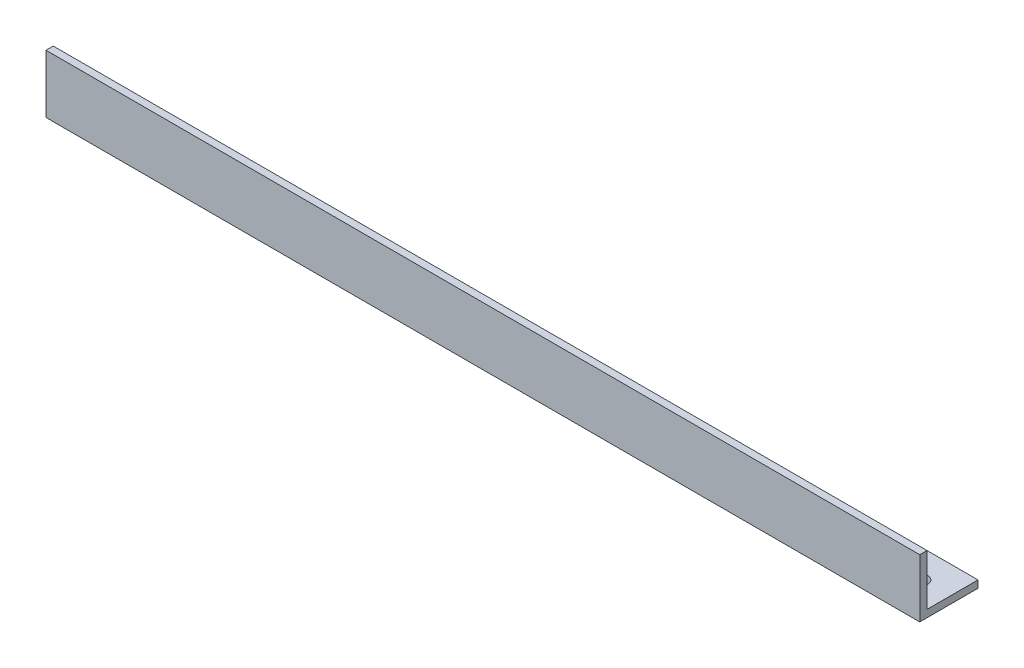
SolidWorks part; units mm, degrees
ref_plane "Front Plane" through (0, 0, 0) normal (0, 0, 1) x (1, 0, 0)
ref_plane "Top Plane" through (0, 0, 0) normal (0, 1, 0) x (1, 0, 0)
ref_plane "Right Plane" through (0, 0, 0) normal (1, 0, 0) x (0, 0, -1)
sketch "Sketch1" plane through (0, 0, 0) normal (1, 0, 0) x (0, 0, -1)
  line L0 (0, 0) -> (25.4, 0)
  line L1 (0, 0) -> (0, 25.4)
  line L2 (0, 25.4) -> (3.175, 25.4)
  line L3 (3.175, 25.4) -> (3.175, 3.175)
  line L4 (3.175, 3.175) -> (25.4, 3.175)
  line L5 (25.4, 3.175) -> (25.4, 0)
  dimension "D1" = 3.175
  dimension "D2" = 3.175
  dimension "D3" = 25.4
  dimension "D4" = 25.4
extrude "Boss-Extrude1" add sketch "Sketch1" along normal blind 381
sketch "Sketch2" plane through (0, 0, 0) normal (0, -1, 0) x (1, 0, 0)
  line L0 (381, 0) -> (381, -25.4) construction
  line L1 (381, -25.4) -> (0, -25.4) construction
  line L2 (0, 0) -> (0, -25.4) construction
  line L3 (0, -25.4) -> (0, -3.175) construction
  line L4 (381, -25.4) -> (0, -25.4) construction
  circle A0 centre (73.66, -12.7) radius 3.429
  circle A1 centre (368.3, -12.7) radius 3.429
  circle A3 centre (19.05, -12.7) radius 3.429
  dimension "D1" = 6.858
  dimension "D2" = 12.7
  dimension "D3" = 12.7
  dimension "D4" = 73.66
  dimension "D6" = 19.05
  dimension "D7" = 12.7
extrude "Cut-Extrude1" cut sketch "Sketch2" against normal up to next
